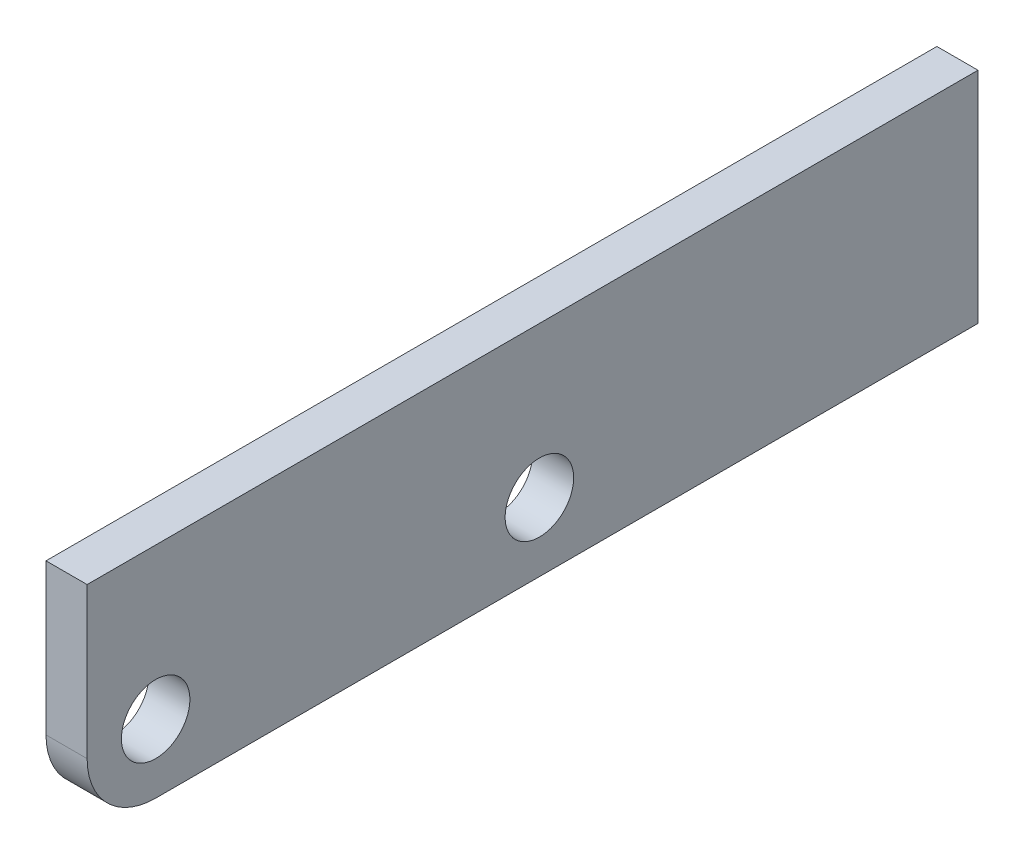
SolidWorks part; units mm, degrees
material "Plain Carbon Steel"
ref_plane "Front Plane" through (0, 0, 0) normal (0, 0, 1) x (1, 0, 0)
ref_plane "Top Plane" through (0, 0, 0) normal (0, 1, 0) x (1, 0, 0)
ref_plane "Right Plane" through (0, 0, 0) normal (1, 0, 0) x (0, 0, -1)
sketch "Sketch1" plane through (0, 0, 0) normal (1, 0, 0) x (0, 0, -1)
  line L1 (-206.375, 50.8) -> (206.375, 50.8)
  line L2 (-206.375, 50.8) -> (-206.375, -50.8)
  line L3 (-206.375, -50.8) -> (206.375, -50.8)
  line L4 (206.375, 50.8) -> (206.375, -50.8)
  line L5 (-206.375, 50.8) -> (206.375, -50.8) construction
  line L6 (-206.375, -50.8) -> (206.375, 50.8) construction
  point P0 (0, 0)
  dimension "D1" = 412.75
  dimension "D2" = 101.6
extrude "Boss-Extrude1" add sketch "Sketch1" along normal mid plane 19.05
sketch "Sketch2" plane through (9.525, 0, 0) normal (1, 0, 0) x (0, 0, -1)
  line L0 (-206.375, 50.8) -> (-206.375, -50.8) construction
  line L2 (3.175, -19.05) -> (-174.625, -19.05) construction
  line L4 (-206.375, -50.8) -> (206.375, -50.8) construction
  circle A0 centre (-174.625, -19.05) radius 15.875
  circle A1 centre (3.175, -19.05) radius 15.875
  dimension "D1" = 31.75
  dimension "D2" = 31.75
  dimension "D3" = 177.8
  dimension "D5" = 31.75
extrude "Cut-Extrude1" cut sketch "Sketch2" against normal up to next
sketch "Sketch3" plane through (0, 50.8, 0) normal (0, 1, 0) x (1, 0, 0)
  line L0 (0, 206.375) -> (0, -206.375) construction
  line L1 (9.525, 206.375) -> (-9.525, 206.375) construction
  line L2 (9.525, -206.375) -> (-9.525, -206.375) construction
fillet "Fillet1" radius 31.75 1 edges at (0, -50.8, 206.375)
